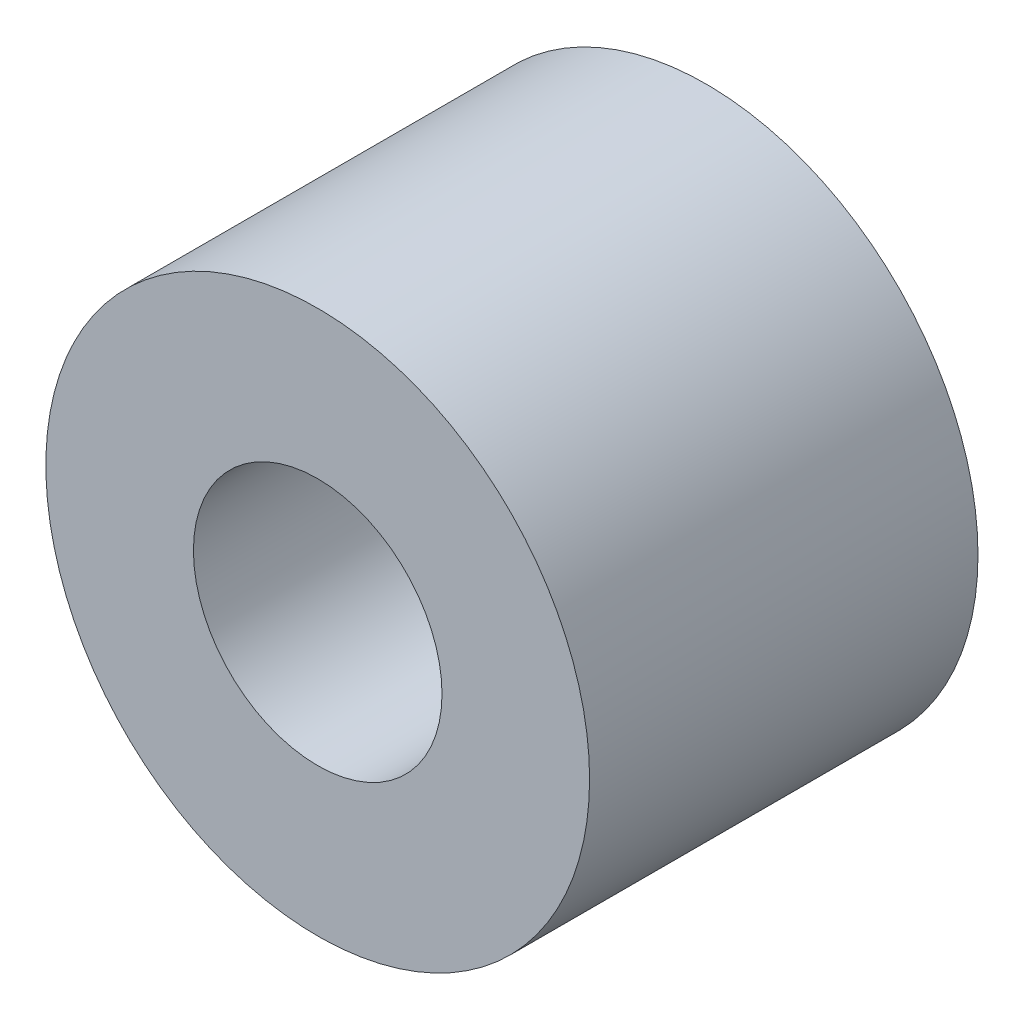
SolidWorks part; units mm, degrees
ref_plane "正面" through (0, 0, 0) normal (0, 0, 1) x (1, 0, 0)
ref_plane "平面" through (0, 0, 0) normal (0, 1, 0) x (1, 0, 0)
ref_plane "右側面" through (0, 0, 0) normal (1, 0, 0) x (0, 0, -1)
sketch "ｽｹｯﾁ1" plane through (0, 0, 0) normal (0, 0, 1) x (1, 0, 0)
  circle A0 centre (0, 0) radius 1.6
  circle A1 centre (0, 0) radius 3.5
  dimension "D1" = 3.2
  dimension "D2" = 7
extrude "ﾎﾞｽ - 押し出し1" add sketch "ｽｹｯﾁ1" along normal blind 5
